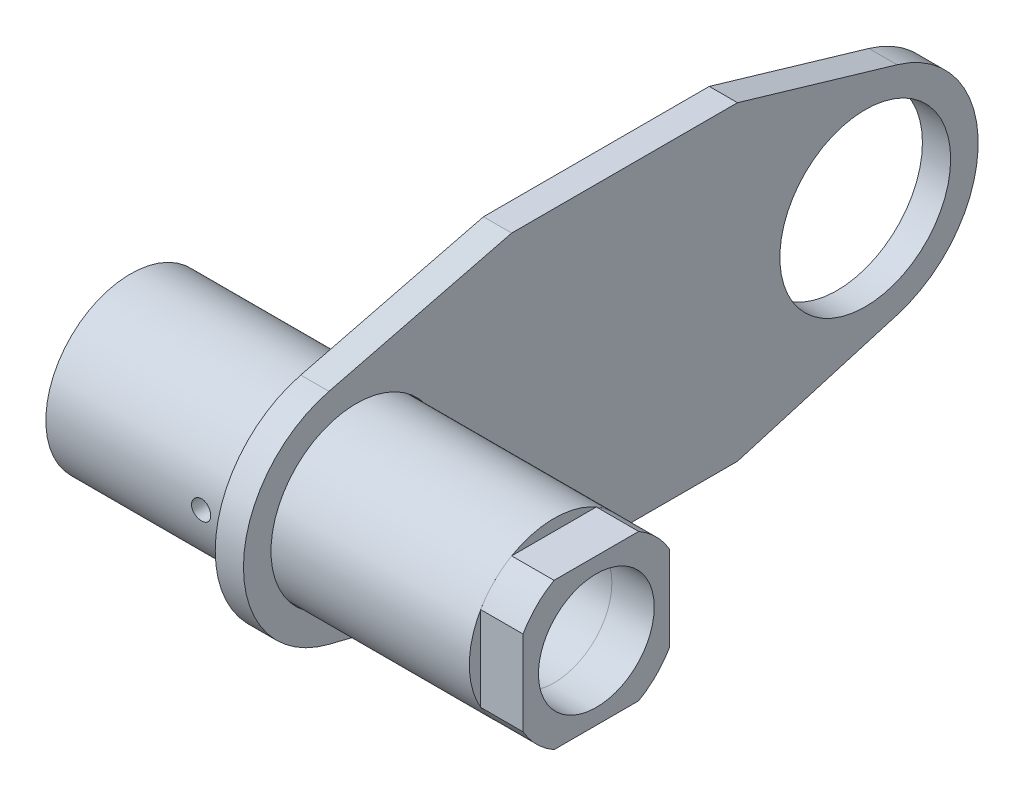
SolidWorks part; units mm, degrees
ref_plane "Plan de face" through (0, 0, 0) normal (0, 0, 1) x (1, 0, 0)
ref_plane "Plan de dessus" through (0, 0, 0) normal (0, 1, 0) x (1, 0, 0)
ref_plane "Plan de droite" through (0, 0, 0) normal (1, 0, 0) x (0, 0, -1)
sketch "Esquisse1" plane through (0, 0, 0) normal (0, 0, 1) x (1, 0, 0)
  line L0 (-75, 0) -> (75, 0)
other "Elément mécano-soudé1"
ref_plane "Plan1" through (-75, 0, 0) normal (1, 0, 0) x (0, 1, 0)
sketch "rond" plane through (-75, 0, 0) normal (1, 0, 0) x (0, 1, 0)
  line L0 (-20.5, 0) -> (20.5, 0) construction
  circle A0 centre (0, 0) radius 20.5
  circle A1 centre (0, 0) radius 30
  point P5 (0, 0)
  dimension "D1" = 60
  dimension "d" = 41
hole_wizard "Trou taraudé M8x1.251" positions "Esquisse3" profile "Esquisse2" tap size "M8x1.25" standard "Ansi Metric"
sketch "Esquisse3" plane through (0, 0, 0) normal (0, 0, 1) x (1, 0, 0)
  line L1 (-75, 30) -> (-75, -30) construction
  point P0 (-20, 0)
  dimension "D1" = 55
sketch "Esquisse2" plane through (-20, 0, 0) normal (1, 0, 0) x (0, 1, 0)
  line L0 (0, 0) -> (0, 30)
  line L1 (0, 30) -> (3.4, 30)
  line L2 (3.4, 30) -> (3.4, 0)
  line L5 (3.4, 0) -> (0, 0)
  line L11 (0, -6.35) -> (0, 107.95) construction
  dimension "Diamètre du trou pour taraudage jusqu'au prochain" = 6.8
  dimension "Profondeur du trou pour taraudage jusqu'au prochain" = 30
cosmetic thread "Filetage de perçage1" parameters "D2"=8
sketch "Esquisse4" plane through (0, 0, 0) normal (0, 0, 1) x (1, 0, 0)
  line L1 (59, 5.1) -> (75, 5.1)
  line L2 (59, 5.1) -> (59, -5.1)
  line L3 (59, -5.1) -> (75, -5.1)
  line L4 (75, 5.1) -> (75, -5.1)
  line L5 (75, -30) -> (75, 30) construction
  point P6 (75, 0)
  dimension "D1" = 16
  dimension "D2" = 10.2
extrude "Enlèv. mat.-Extru.1" [suppressed] cut sketch "Esquisse4" against normal through all
sketch "Esquisse5" plane through (75, 0, 0) normal (1, 0, 0) x (0, 0, -1)
  line L0 (-15, 25.9808) -> (15, 25.9808)
  line L1 (-25.9808, 15) -> (-25.9808, -15)
  line L2 (-15, -25.9808) -> (15, -25.9808)
  line L3 (25.9808, -15) -> (25.9808, 15)
  circle A4 centre (0, 0) radius 30 construction
  arc A5 (25.9808, 15) -> (25.9808, -15) centre (0, 0) ccw
  dimension "D1" = 30
extrude "Boss.-Extru.1" add sketch "Esquisse5" along normal blind 15 separate body
sketch "Esquisse6" plane through (75, 0, 0) normal (1, 0, 0) x (0, 0, -1)
  circle A0 centre (0, 0) radius 40
  circle A1 centre (0, 0) radius 30.25
  dimension "D1" = 60.5
  dimension "D2" = 80
extrude "Boss.-Extru.2" add sketch "Esquisse6" against normal blind 10 from offset 70 separate body offset against normal yes
sketch "Esquisse7" plane through (5, 0, 0) normal (1, 0, 0) x (0, 0, -1)
  line L0 (0, 0) -> (180.25, 0) construction
  line L1 (135, 55) -> (135, -55) construction
  line L2 (55, 55) -> (55, -55) construction
  line L3 (-9.7121, 38.803) -> (55, 55)
  line L4 (55, 55) -> (135, 55)
  line L5 (135, 55) -> (191.5347, 38.3752)
  line L6 (191.5347, -38.3752) -> (135, -55)
  line L7 (135, -55) -> (55, -55)
  line L8 (55, -55) -> (-9.7121, -38.803)
  circle A0 centre (0, 0) radius 30.25 construction
  circle A1 centre (0, 0) radius 40 construction
  circle A2 centre (0, 0) radius 30.25
  circle A3 centre (0, 0) radius 40
  circle A4 centre (180.25, 0) radius 30.25
  circle A5 centre (180.25, 0) radius 40
  point P10 (135, 0)
  circle M4 centre (0, 0) radius 30.25
  circle M5 centre (0, 0) radius 40
  dimension "D4" = 15
  dimension "D1" = 15
  dimension "D2" = 135
  dimension "D3" = 110
extrude "Boss.-Extru.3" add sketch "Esquisse7" against normal blind 10 separate body contours A5 L5 L4 L3 L8 L7 L6 M5 | A5 A4 | M5 M4
delete or keep bodies "Corps-Supprimer/Garder 1" type delete bodies bodies 105
